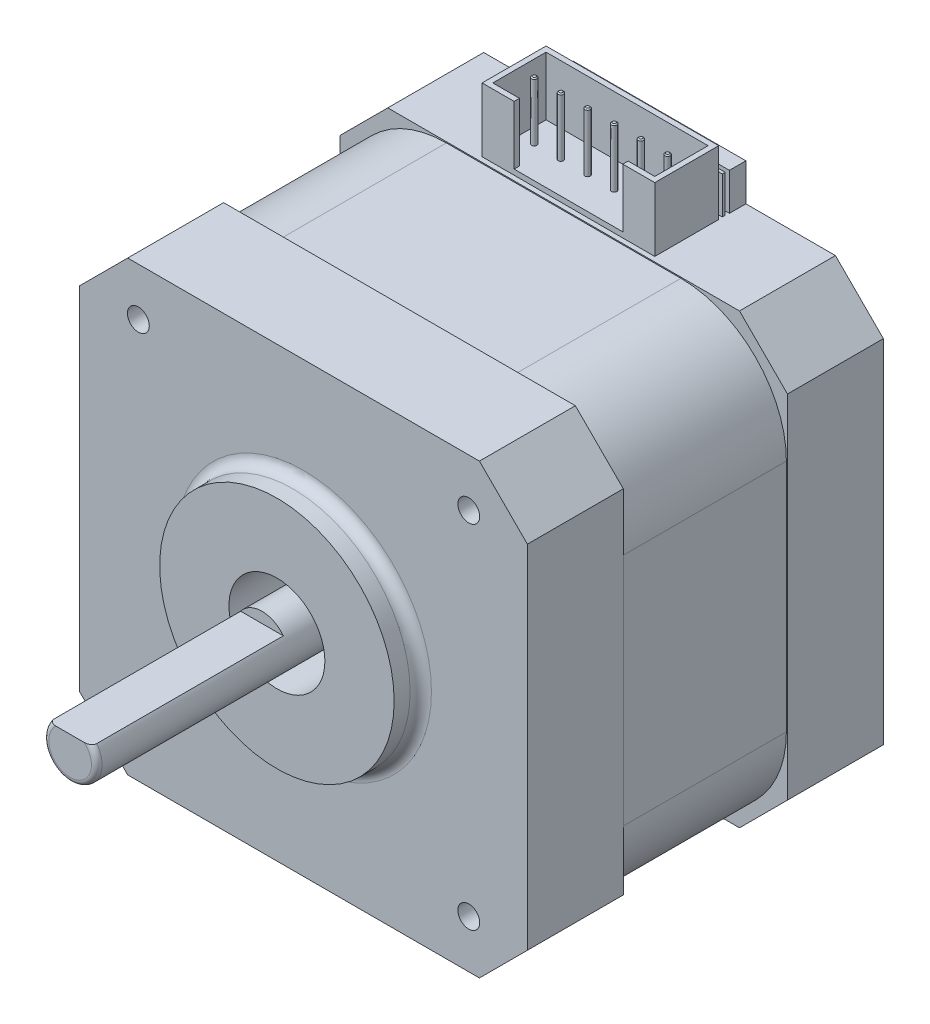
SolidWorks part; units mm, degrees
ref_plane "Front Plane" through (0, 0, 0) normal (0, 0, 1) x (1, 0, 0)
ref_plane "Top Plane" through (0, 0, 0) normal (0, 1, 0) x (1, 0, 0)
ref_plane "Right Plane" through (0, 0, 0) normal (1, 0, 0) x (0, 0, -1)
sketch "Sketch1" plane through (0, 0, 0) normal (0, 0, 1) x (1, 0, 0)
  line L0 (21, 16.5) -> (16.5, 21)
  line L1 (16.5, -21) -> (-16.5, -21)
  line L2 (21, -16.5) -> (21, 16.5)
  line L3 (16.5, 21) -> (-16.5, 21)
  line L4 (-21, -16.5) -> (-21, 16.5)
  line L5 (21, -21) -> (-21, 21) construction
  line L6 (21, 21) -> (-21, -21) construction
  line L7 (-16.5, 21) -> (-21, 16.5)
  line L8 (-16.5, -21) -> (-21, -16.5)
  line L9 (21, -16.5) -> (16.5, -21)
  point P0 (0, 0)
  dimension "D1" = 42
  dimension "D2" = 42
extrude "Boss-Extrude1" add sketch "Sketch1" along normal blind 9
sketch "Sketch2" plane through (0, 0, 9) normal (0, 0, 1) x (1, 0, 0)
  line L0 (16.5, 21) -> (-16.5, 21) construction
  line L1 (11, -21) -> (-11, -21) construction
  line L2 (21, -11) -> (21, 11) construction
  line L3 (11, 21) -> (-11, 21) construction
  line L4 (-21, -11) -> (-21, 11) construction
  line L5 (21, -21) -> (-21, 21) construction
  line L6 (21, 21) -> (-21, -21) construction
  line L7 (-21, 16.5) -> (-21, -16.5) construction
  line L8 (11, 20.9) -> (-11, 20.9)
  line L9 (-20.9, -11) -> (-20.9, 11)
  line L10 (11, -20.9) -> (-11, -20.9)
  line L11 (20.9, -11) -> (20.9, 11)
  arc A0 (-11, -21) -> (-21, -11) centre (-11, -11) cw construction
  arc A1 (11, -21) -> (21, -11) centre (11, -11) ccw construction
  arc A2 (21, 11) -> (11, 21) centre (11, 11) ccw construction
  arc A3 (-11, 21) -> (-21, 11) centre (-11, 11) ccw construction
  arc A4 (-11, 20.9) -> (-20.9, 11) centre (-11, 11) ccw
  arc A5 (-11, -20.9) -> (-20.9, -11) centre (-11, -11) cw
  arc A6 (11, -20.9) -> (20.9, -11) centre (11, -11) ccw
  arc A7 (20.9, 11) -> (11, 20.9) centre (11, 11) ccw
  point P0 (0, 0)
  dimension "D1" = 10
  dimension "D2" = 0.1
extrude "Boss-Extrude2" add sketch "Sketch2" along normal blind 15.4
sketch "Sketch3" plane through (0, 0, 24.4) normal (0, 0, 1) x (1, 0, 0)
  line L8 (21, -16.5) -> (21, 16.5)
  line L9 (16.5, -21) -> (21, -16.5)
  line L10 (-16.5, -21) -> (16.5, -21)
  line L11 (-21, -16.5) -> (-16.5, -21)
  line L12 (-21, 16.5) -> (-21, -16.5)
  line L13 (-16.5, 21) -> (-21, 16.5)
  line L14 (16.5, 21) -> (-16.5, 21)
  line L15 (21, 16.5) -> (16.5, 21)
  line L16 (21, -16.5) -> (21, 16.5)
  line L17 (16.5, -21) -> (21, -16.5)
  line L18 (-16.5, -21) -> (16.5, -21)
  line L19 (-21, -16.5) -> (-16.5, -21)
  line L20 (-21, 16.5) -> (-21, -16.5)
  line L21 (-16.5, 21) -> (-21, 16.5)
  line L22 (16.5, 21) -> (-16.5, 21)
  line L23 (21, 16.5) -> (16.5, 21)
  dimension "D1" = 0
extrude "Boss-Extrude3" add sketch "Sketch3" along normal blind 9
sketch "Sketch4" plane through (0, 0, 33.4) normal (0, 0, 1) x (1, 0, 0)
  circle A0 centre (0, 0) radius 4.5
  dimension "D1" = 9
extrude "Cut-Extrude1" cut sketch "Sketch4" against normal blind 5
sketch "Sketch5" plane through (0, 0, 28.4) normal (0, 0, 1) x (1, 0, 0)
  circle A0 centre (0, 0) radius 2.5
  dimension "D1" = 5
extrude "Boss-Extrude4" add sketch "Sketch5" along normal blind 26.9
sketch "Sketch6" plane through (0, 21, 0) normal (0, 1, 0) x (1, 0, 0)
  line L0 (16.5, 0) -> (-16.5, 0) construction
  line L1 (-8.1, 0) -> (8.1, 0)
  line L2 (-8.1, 0) -> (-8.1, -1.5474)
  line L3 (-8.1, -1.5474) -> (8.1, -1.5474)
  line L4 (8.1, 0) -> (8.1, -1.5474)
  dimension "D1" = 16.2
extrude "Boss-Extrude5" add sketch "Sketch6" along normal blind 3.5
sketch "Sketch7" plane through (0, 21, 0) normal (0, 1, 0) x (1, 0, 0)
  line L0 (-8.1, -1.5474) -> (8.1, -1.5474) construction
  line L1 (-8.1, -2.5474) -> (8.1, -2.5474)
  line L2 (-8.1, -2.5474) -> (-8.1, -8.5474)
  line L3 (-8.1, -8.5474) -> (-5.1, -8.5474)
  line L4 (8.1, -2.5474) -> (8.1, -8.5474)
  line L5 (8.1, -8.5474) -> (5.1, -8.5474)
  dimension "D1" = 6
  dimension "D2" = 1
extrude "Extrude-Thin4" add sketch "Sketch7" along normal blind 6 thin
sketch "Sketch8" plane through (0, 21, 0) normal (0, 1, 0) x (1, 0, 0)
  line L0 (-5.1, -8.0474) -> (-5.1, -8.5474)
  line L1 (-7.6, -3.0474) -> (7.6, -3.0474)
  line L2 (-7.6, -3.0474) -> (-7.6, -8.0474)
  line L3 (5.1, -8.0474) -> (7.6, -8.0474)
  line L4 (7.6, -3.0474) -> (7.6, -8.0474)
  line L5 (-5.1, -8.5474) -> (5.1, -8.5474)
  line L6 (5.1, -8.5474) -> (5.1, -8.0474)
  line L8 (-7.6, -8.0474) -> (-5.1, -8.0474)
extrude "Boss-Extrude7" add sketch "Sketch8" along normal blind 0.5
sketch "Sketch9" plane through (0, 21, 0) normal (0, 1, 0) x (1, 0, 0)
  line L1 (8.0618, -2.1768) -> (-8.0618, -2.1768)
  line L2 (8.0618, -2.1768) -> (8.0618, -1.9027)
  line L3 (8.0618, -1.9027) -> (-8.0618, -1.9027)
  line L4 (-8.0618, -2.1768) -> (-8.0618, -1.9027)
  line L5 (8.0618, -2.1768) -> (-8.0618, -1.9027) construction
  line L6 (8.0618, -1.9027) -> (-8.0618, -2.1768) construction
  point P0 (0, -2.0397)
extrude "Boss-Extrude8" add sketch "Sketch9" along normal up to vertex (3.5 mm away)
sketch "Sketch10" plane through (0, 21.5, 0) normal (0, 1, 0) x (1, 0, 0)
  circle A0 centre (-6.2046, -5.5474) radius 0.25
  circle A1 centre (-3.7046, -5.5474) radius 0.25
  circle A2 centre (-1.2046, -5.5474) radius 0.25
  circle A3 centre (1.2954, -5.5474) radius 0.25
  circle A4 centre (3.7954, -5.5474) radius 0.25
  circle A5 centre (6.2954, -5.5474) radius 0.25
  dimension "D1" = 0.5
  dimension "D2" = 6
extrude "Boss-Extrude9" add sketch "Sketch10" along normal up to vertex (5.5 mm away)
chamfer "Chamfer1" distance 0.1 angle 45 6 edges at (6.2954, 27, 5.7974) (3.7954, 27, 5.7974) (1.2954, 27, 5.7974) (-1.2046, 27, 5.7974) (-3.7046, 27, 5.7974) (-6.2046, 27, 5.7974)
sketch "Sketch11" plane through (0, 0, 33.4) normal (0, 0, 1) x (1, 0, 0)
  circle A0 centre (0, 0) radius 11
  circle A1 centre (0, 0) radius 4.5 construction
  circle A2 centre (0, 0) radius 4.5
  dimension "D1" = 22
extrude "Boss-Extrude10" add sketch "Sketch11" along normal blind 2.5
fillet "Fillet1" radius 1 1 edges at (11, 0, 33.4)
sketch "Sketch12" plane through (0, 0, 55.3) normal (0, 0, 1) x (1, 0, 0)
  line L0 (2, 1.5) -> (-2, 1.5)
  circle A0 centre (0, 0) radius 2.5 construction
  arc A2 (-2, 1.5) -> (2, 1.5) centre (0, 0) cw
extrude "Cut-Extrude2" cut sketch "Sketch12" against normal blind 18
fillet "Fillet2" radius 0.5 1 edges at (0, -2.5, 55.3)
hole_wizard "Tap Drill for M2.5x0.45 Tap2" positions "Sketch15" profile "Sketch14" hole size "M2.5x0.45" standard "ANSI Metric"
sketch "Sketch15" plane through (0, 0, 33.4) normal (0, 0, 1) x (1, 0, 0)
  line L0 (-21, 16.5) -> (-21, -16.5) construction
  line L1 (16.5, 21) -> (-16.5, 21) construction
  line L2 (21, -16.5) -> (21, 16.5) construction
  line L3 (-16.5, -21) -> (16.5, -21) construction
  point P0 (15.5, 16.5)
  point P2 (15.5, -16.5)
  point P4 (-15.5, -16.5)
  point P6 (-15.5, 16.5)
  dimension "D1" = 5.5
  dimension "D2" = 4.5
  dimension "D3" = 4.5
  dimension "D4" = 5.5
  dimension "D5" = 5.5
  dimension "D6" = 4.5
  dimension "D7" = 4.5
  dimension "D8" = 5.5
sketch "Sketch14" plane through (15.5, 16.5, 33.4) normal (1, 0, 0) x (0, -1, 0)
  line L0 (0, 0) -> (0, 5.6159)
  line L1 (0, 5.6159) -> (1.025, 5)
  line L2 (1.025, 5) -> (1.025, 0)
  line L5 (1.025, 0) -> (0, 0)
  line L10 (0, 5.6159) -> (-1.025, 5) construction
  line L11 (0, -6.35) -> (0, 107.95) construction
  dimension "Hole Dia." = 2.05
  dimension "Hole Depth" = 5
  dimension "Drill Angle" = 118
